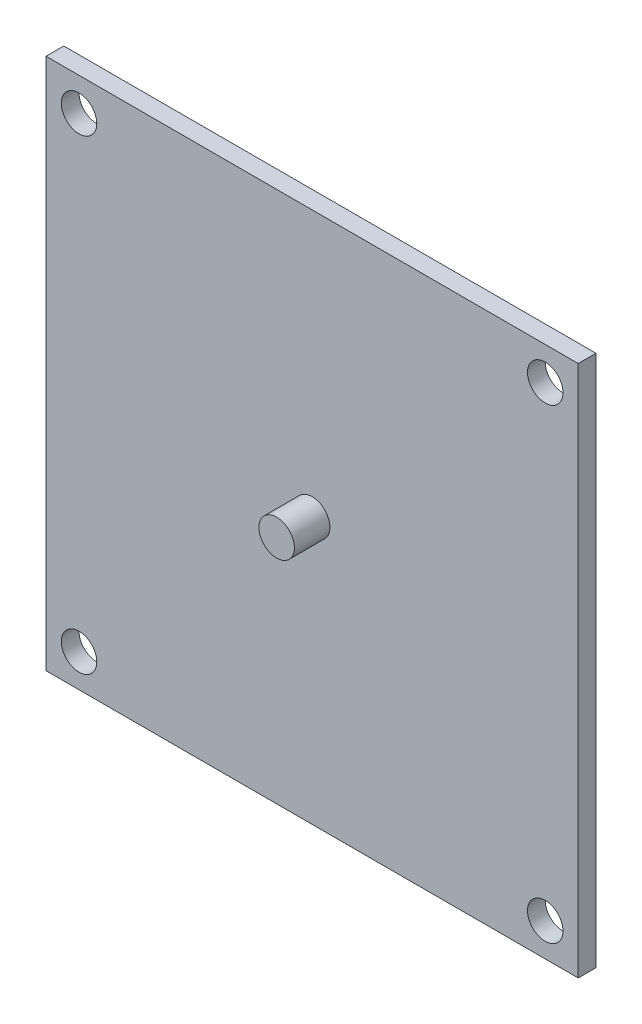
SolidWorks part; units mm, degrees
ref_plane "Front Plane" through (0, 0, 0) normal (0, 0, 1) x (1, 0, 0)
ref_plane "Top Plane" through (0, 0, 0) normal (0, 1, 0) x (1, 0, 0)
ref_plane "Right Plane" through (0, 0, 0) normal (1, 0, 0) x (0, 0, -1)
sketch "Sketch1" plane through (0, 0, 0) normal (0, 0, 1) x (1, 0, 0)
  line L1 (-15, 15) -> (15, 15)
  line L2 (-15, 15) -> (-15, -15)
  line L3 (-15, -15) -> (15, -15)
  line L4 (15, 15) -> (15, -15)
  line L5 (-15, 15) -> (15, -15) construction
  line L6 (-15, -15) -> (15, 15) construction
  point P0 (0, 0)
  dimension "D1" = 30
  dimension "D2" = 30
extrude "Boss-Extrude1" add sketch "Sketch1" along normal blind 1
sketch "Sketch2" plane through (0, 0, 1) normal (0, 0, 1) x (1, 0, 0)
  line L0 (-15, 15) -> (-15, -15) construction
  line L1 (15, 15) -> (-15, 15) construction
  circle A0 centre (-13.14, 13.14) radius 1
  circle A1 centre (13.14, 13.14) radius 1
  circle A2 centre (13.14, -13.14) radius 1
  circle A3 centre (-13.14, -13.14) radius 1
  point P15 (0, 0)
  dimension "D1" = 2
  dimension "D2" = 1.86
  dimension "D3" = 1.86
  dimension "D4" = 4
extrude "Cut-Extrude1" cut sketch "Sketch2" against normal through all
sketch "Sketch3" plane through (0, 0, 1) normal (0, 0, 1) x (1, 0, 0)
  circle A0 centre (0, 0) radius 1
  dimension "D1" = 2
extrude "Boss-Extrude2" add sketch "Sketch3" along normal blind 2
